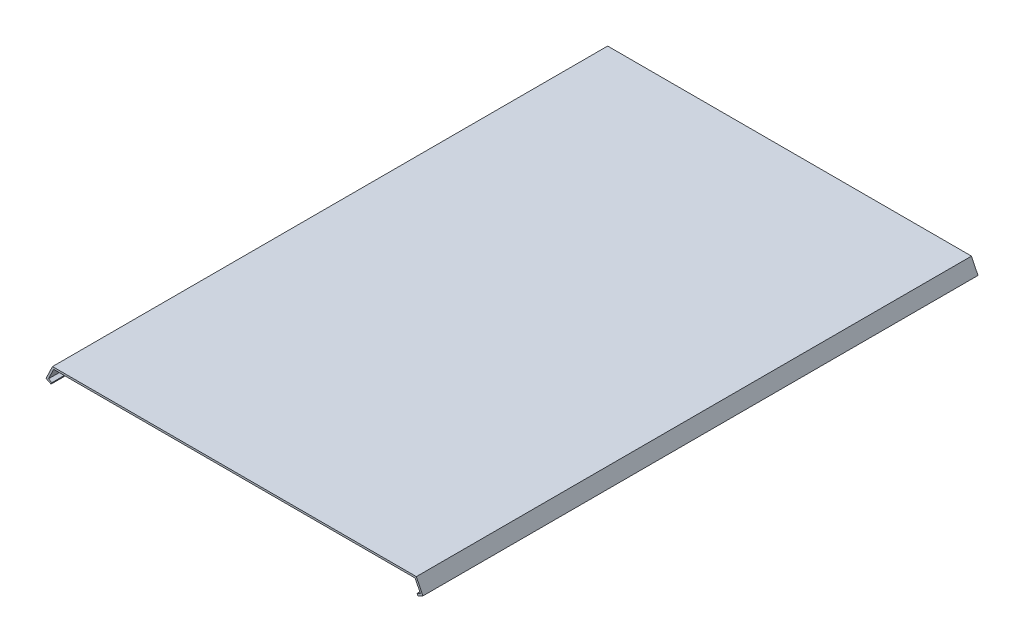
SolidWorks part; units mm, degrees
material "PA 6/6 polyamide Type 6-6 (Nylon)"
ref_plane "Plan de face" through (0, 0, 0) normal (0, 0, 1) x (1, 0, 0)
ref_plane "Plan de dessus" through (0, 0, 0) normal (0, 1, 0) x (1, 0, 0)
ref_plane "Plan de droite" through (0, 0, 0) normal (1, 0, 0) x (0, 0, -1)
sketch "Esquisse1" plane through (0, 0, 0) normal (0, 0, 1) x (1, 0, 0)
  line L0 (-97, 0) -> (97, 0) construction
  line L1 (-97, 0) -> (-182.5, -177.5) construction
  line L2 (-182.5, -177.5) -> (-182.5, -182.5) construction
  line L3 (0, 0) -> (0, -1) construction
  line L4 (0, -182.5) -> (0, -1) construction
  line L5 (-182.5, -182.5) -> (182.5, -182.5) construction
  line L6 (182.5, -182.5) -> (182.5, -177.5) construction
  line L7 (-96.3717, -1) -> (-99.1368, -6.7405)
  line L8 (-99.1368, -6.7405) -> (-97.335, -7.6084)
  line L9 (97, 0) -> (182.5, -177.5) construction
  line L10 (-97, 0) -> (-100.4717, -7.2074)
  line L11 (-100.4717, -7.2074) -> (-97.769, -8.5093)
  line L12 (-97.335, -7.6084) -> (-97.769, -8.5093)
  line L13 (-96.3717, -1) -> (96.3717, -1)
  line L14 (96.3717, -1) -> (99.1368, -6.7405)
  line L15 (97.769, -8.5093) -> (100.4717, -7.2074)
  line L16 (100.4717, -7.2074) -> (97, 0)
  line L17 (97, 0) -> (-97, 0)
  line L18 (99.1368, -6.7405) -> (97.335, -7.6084)
  line L19 (97.335, -7.6084) -> (97.769, -8.5093)
  point P17 (0, 0)
  point P18 (0, 0)
  point P21 (0, 0)
  dimension "D1" = 365
  dimension "D2" = 10
  dimension "D3" = 194
  dimension "D4" = 365
  dimension "D5" = 1
  dimension "D6" = 8
  dimension "D7" = 1
  dimension "D8" = 1
  dimension "D9" = 3
  dimension "D10" = 1
extrude "Extrusion1" add sketch "Esquisse1" along normal mid plane 296
